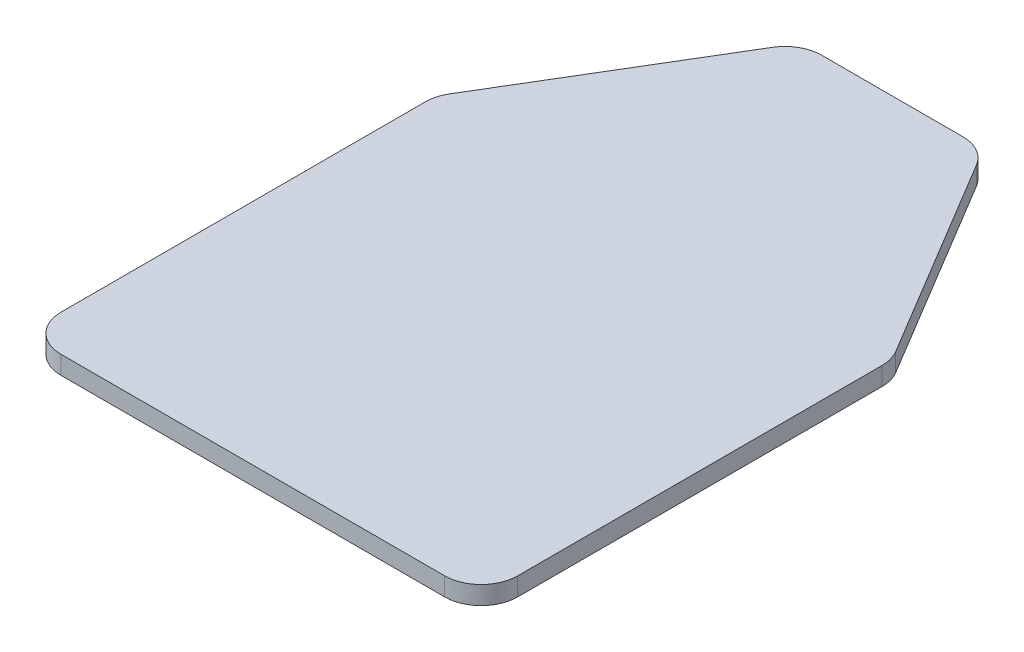
SolidWorks part; units mm, degrees
ref_plane "Спереди" through (0, 0, 0) normal (0, 0, 1) x (1, 0, 0)
ref_plane "Сверху" through (0, 0, 0) normal (0, 1, 0) x (1, 0, 0)
ref_plane "Справа" through (0, 0, 0) normal (1, 0, 0) x (0, 0, -1)
sketch "Эскиз1" plane through (0, 0, 0) normal (0, 1, 0) x (1, 0, 0)
  line L0 (210, 0) -> (-210, 0)
  line L1 (-250, 40) -> (-250, 438.9206)
  line L2 (0, -32.5256) -> (0, 666.4302) construction
  line L3 (-244.2997, 459.5005) -> (-111.6521, 680.5798)
  line L4 (-77.3524, 700) -> (77.3524, 700)
  line L5 (244.2997, 459.5005) -> (111.6521, 680.5798)
  line L6 (250, 40) -> (250, 438.9206)
  arc A0 (-210, 0) -> (-250, 40) centre (-210, 40) cw
  arc A1 (-250, 438.9206) -> (-244.2997, 459.5005) centre (-210, 438.9206) cw
  arc A2 (-111.6521, 680.5798) -> (-77.3524, 700) centre (-77.3524, 660) cw
  arc A3 (111.6521, 680.5798) -> (77.3524, 700) centre (77.3524, 660) ccw
  arc A4 (250, 438.9206) -> (244.2997, 459.5005) centre (210, 438.9206) ccw
  arc A5 (210, 0) -> (250, 40) centre (210, 40) ccw
  point P0 (100, 700)
  point P7 (0, 0)
  point P12 (-250, 0)
  point P15 (-250, 450)
  point P18 (-100, 700)
  point P30 (0, 700)
  point P31 (250, 450)
  point P32 (250, 0)
  dimension "D5" = 40
  dimension "D1" = 450
  dimension "D2" = 700
  dimension "D3" = 250
  dimension "D4" = 100
extrude "Бобышка-Вытянуть1" add sketch "Эскиз1" along normal blind 20
